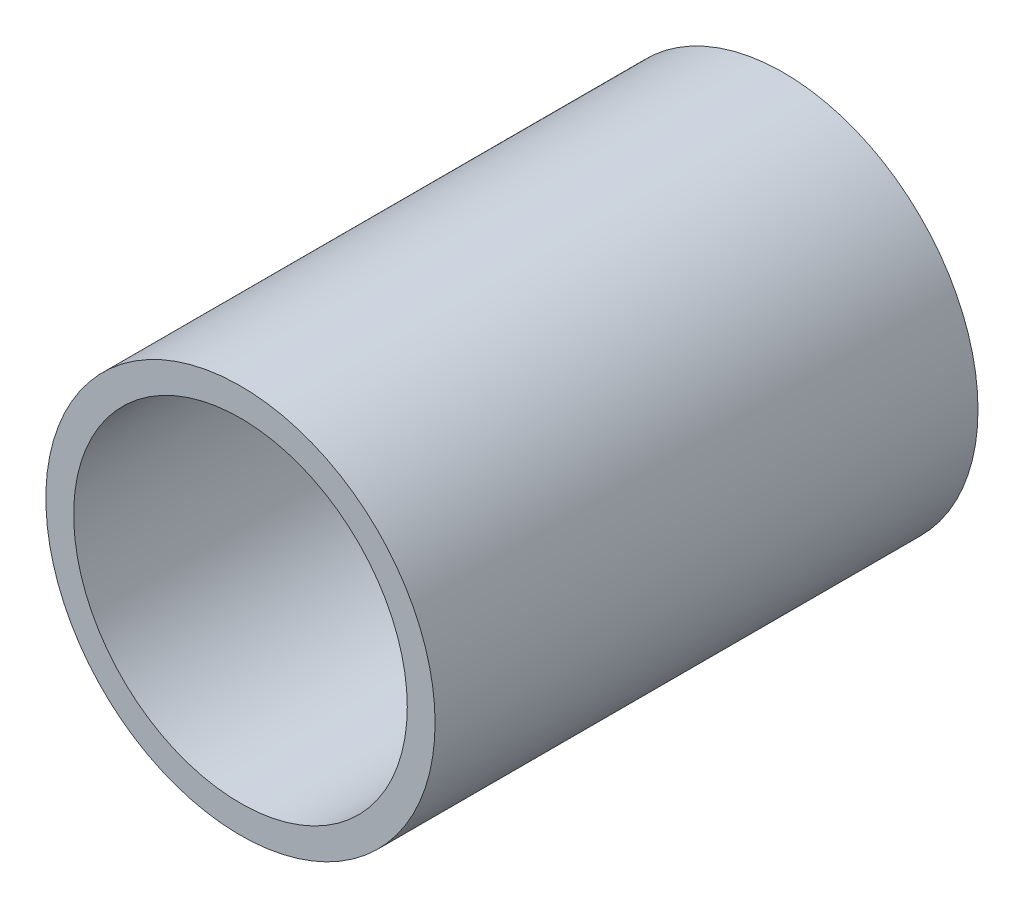
SolidWorks part; units mm, degrees
material "ABS PC"
ref_plane "Front Plane" through (0, 0, 0) normal (0, 0, 1) x (1, 0, 0)
ref_plane "Top Plane" through (0, 0, 0) normal (0, 1, 0) x (1, 0, 0)
ref_plane "Right Plane" through (0, 0, 0) normal (1, 0, 0) x (0, 0, -1)
sketch "Sketch1" plane through (0, 0, 0) normal (0, 0, 1) x (1, 0, 0)
  circle A0 centre (0, 0) radius 44.45
  circle A1 centre (0, 0) radius 38.1
  dimension "D1" = 88.9
  dimension "D2" = 76.2
extrude "Boss-Extrude1" add sketch "Sketch1" along normal mid plane 124
